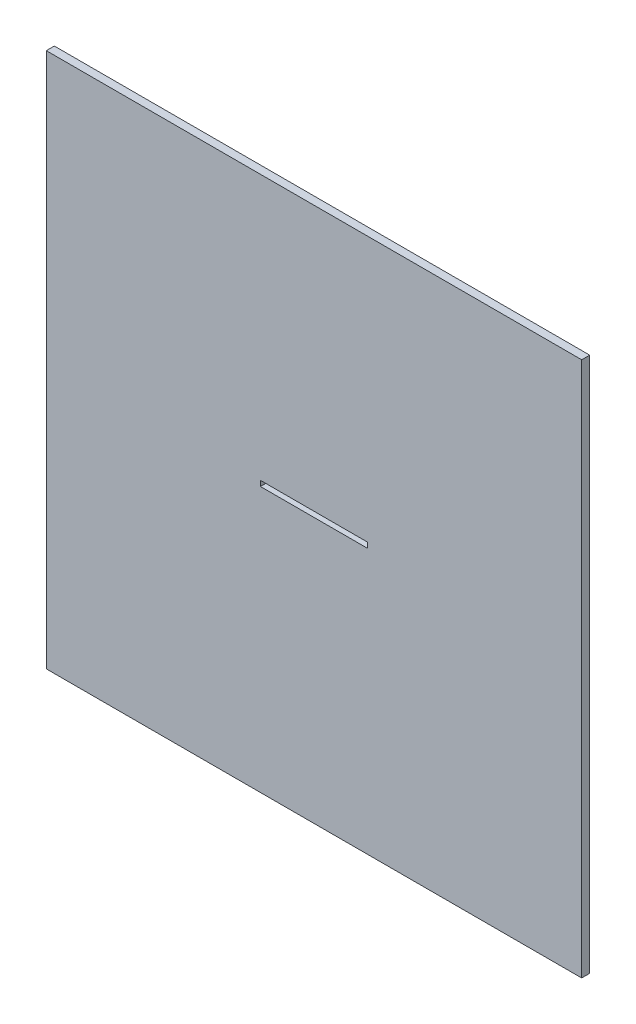
SolidWorks part; units mm, degrees
material "Cedro"
ref_plane "Plano frontal" through (0, 0, 0) normal (0, 0, 1) x (1, 0, 0)
ref_plane "Plano superior" through (0, 0, 0) normal (0, 1, 0) x (1, 0, 0)
ref_plane "Plano direito" through (0, 0, 0) normal (1, 0, 0) x (0, 0, -1)
sketch "Esboço1" plane through (0, 0, 0) normal (0, 0, 1) x (1, 0, 0)
  line L1 (500, -500) -> (-500, -500)
  line L2 (500, -500) -> (500, 500)
  line L3 (500, 500) -> (-500, 500)
  line L4 (-500, -500) -> (-500, 500)
  line L5 (500, -500) -> (-500, 500) construction
  line L6 (500, 500) -> (-500, -500) construction
  point P0 (0, 0)
  dimension "D1" = 1000
  dimension "D2" = 1000
extrude "Ressalto-extrusão1" add sketch "Esboço1" along normal blind 15
sketch "Esboço2" plane through (0, 0, 15) normal (0, 0, 1) x (1, 0, 0)
  line L0 (-100, 0) -> (-500, 0) construction
  line L1 (100, -5) -> (-100, -5)
  line L2 (100, -5) -> (100, 5)
  line L3 (100, 5) -> (-100, 5)
  line L4 (-100, -5) -> (-100, 5)
  line L5 (-500, 500) -> (-500, -500) construction
  line L6 (0, -5) -> (0, -500) construction
  line L7 (-500, -500) -> (500, -500) construction
  dimension "D1" = 10
  dimension "D2" = 200
extrude "Corte-extrusão1" cut sketch "Esboço2" against normal through all
